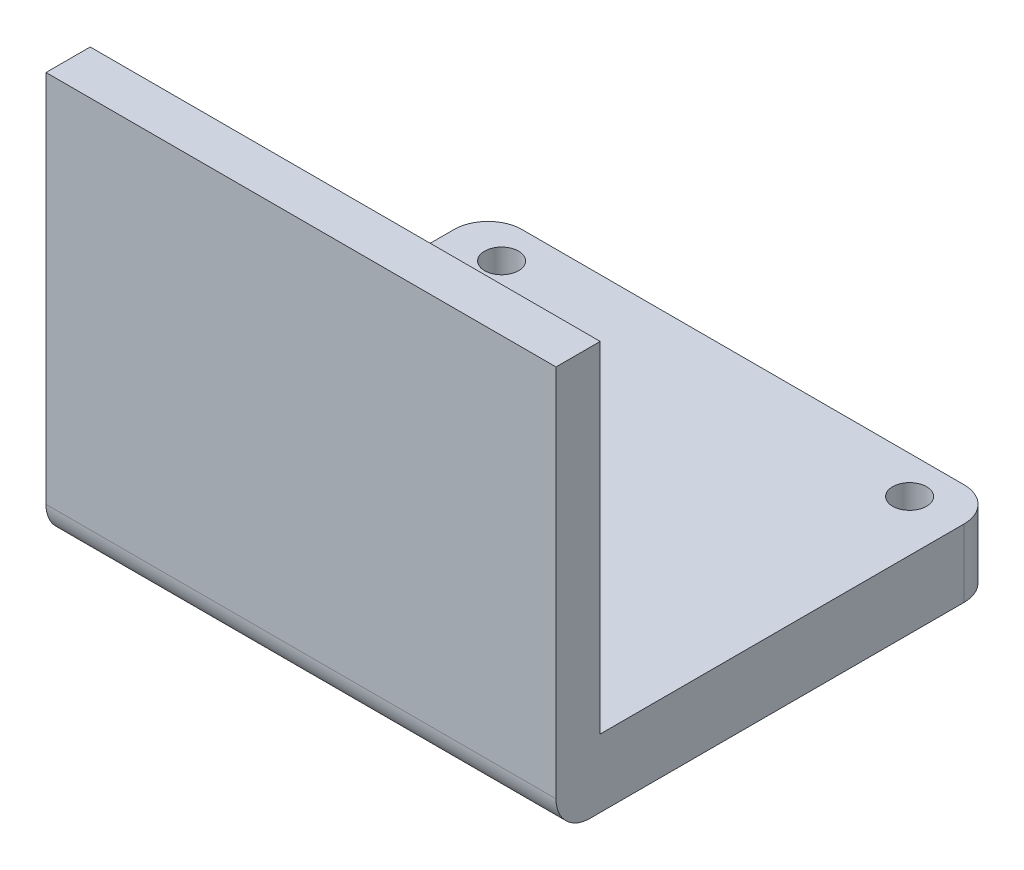
SolidWorks part; units mm, degrees
ref_plane "Front Plane" through (0, 0, 0) normal (0, 0, 1) x (1, 0, 0)
ref_plane "Top Plane" through (0, 0, 0) normal (0, 1, 0) x (1, 0, 0)
ref_plane "Right Plane" through (0, 0, 0) normal (1, 0, 0) x (0, 0, -1)
sketch "Sketch1" plane through (0, 0, 0) normal (0, 1, 0) x (1, 0, 0)
  line L1 (-37.5, -27.5) -> (37.5, -27.5)
  line L2 (-37.5, -27.5) -> (-37.5, 27.5)
  line L3 (-37.5, 27.5) -> (37.5, 27.5)
  line L4 (37.5, -27.5) -> (37.5, 27.5)
  line L5 (-37.5, -27.5) -> (37.5, 27.5) construction
  line L6 (-37.5, 27.5) -> (37.5, -27.5) construction
  circle A0 centre (-30, 22) radius 2.5
  circle A1 centre (30, 22) radius 2.5
  circle A2 centre (0, -18) radius 2.5
  point P0 (0, 0)
  dimension "D3" = 5
  dimension "D4" = 5
  dimension "D5" = 5
  dimension "D1" = 75
  dimension "D2" = 55
  dimension "D6" = 7.5
  dimension "D7" = 7.5
  dimension "D8" = 30
  dimension "D9" = 40
extrude "Boss-Extrude1" add sketch "Sketch1" along normal blind 10 contours L3 L4 L1 L2
sketch "Sketch7" plane through (0, 0, 0) normal (0, 1, 0) x (1, 0, 0)
  line L5 (-37.5, -27.5) -> (37.5, -27.5)
  line L6 (-37.5, -27.5) -> (-37.5, -37.5)
  line L7 (-37.5, -37.5) -> (37.5, -37.5)
  line L8 (37.5, -27.5) -> (37.5, -37.5)
  dimension "D1" = 10
  dimension "D2" = 75
extrude "Boss-Extrude2" add sketch "Sketch7" along normal blind 60
sketch "Sketch9" plane through (0, 60, 0) normal (0, 1, 0) x (1, 0, 0)
  line L0 (37.5, -37.5) -> (37.5, -27.5) construction
  line L1 (-37.5, -27.5) -> (37.5, -27.5)
  line L2 (-37.5, -27.5) -> (-37.5, -31)
  line L3 (-37.5, -31) -> (37.5, -31)
  line L4 (37.5, -27.5) -> (37.5, -31)
  dimension "D1" = 3.5
extrude "Cut-Extrude5" cut sketch "Sketch9" against normal blind 50
fillet "Fillet3" radius 5 1 edges at (0, 0, 37.5)
fillet "Fillet4" radius 5 2 edges at (37.5, 5, -27.5) (-37.5, 5, -27.5)
